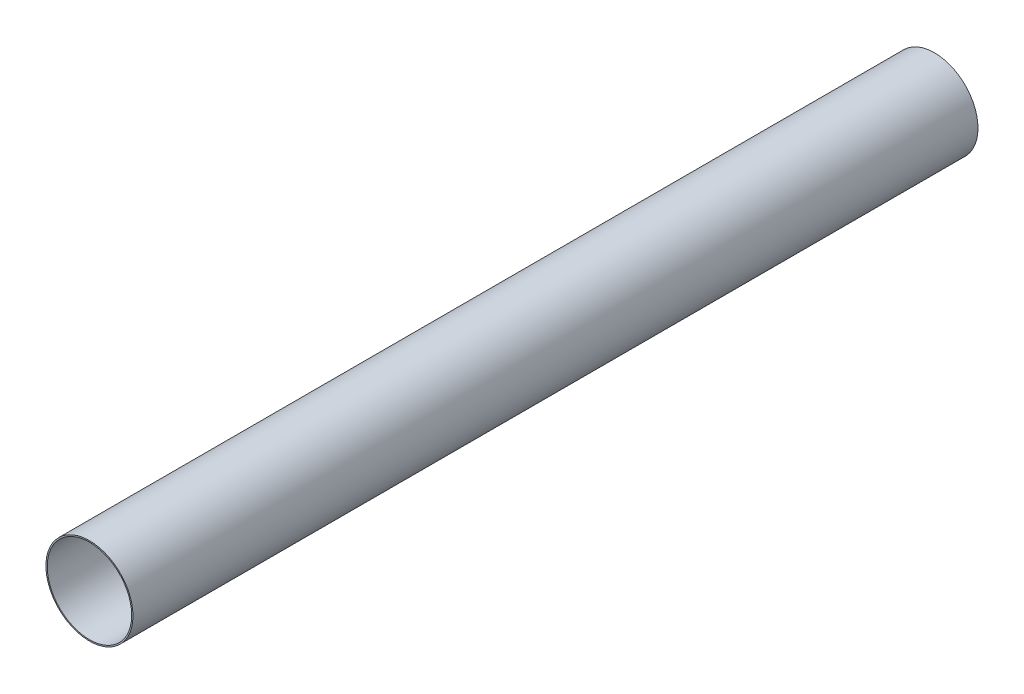
SolidWorks part; units mm, degrees
ref_plane "Front Plane" through (0, 0, 0) normal (0, 0, 1) x (1, 0, 0)
ref_plane "Top Plane" through (0, 0, 0) normal (0, 1, 0) x (1, 0, 0)
ref_plane "Right Plane" through (0, 0, 0) normal (1, 0, 0) x (0, 0, -1)
sketch "Sketch1" plane through (0, 0, 0) normal (0, 0, 1) x (1, 0, 0)
  circle A0 centre (0, 0) radius 39.2557
  circle A1 centre (0, 0) radius 38.1
  dimension "D1" = 76.2
  dimension "D2" = 78.5114
extrude "Boss-Extrude1" add sketch "Sketch1" along normal mid plane 762
equation "\"AIRFRAME_OD\"= 3.091in"
equation "\"AIRFRAME_ID\"= 3.00in"
equation "\"FLAT_T\"= 0.125in"
equation "\"NOSE_EXP_L\"= 3.5in"
equation "\"NOSE_SHOULDER_L\"= 5in"
equation "\"MAIN_L\"= 30in"
equation "\"RECO_COUP_L\"= 6in"
equation "\"RECO_SWITCH_L\"= 1.5in"
equation "\"DROGUE_L\"= 14in"
equation "\"ATS_FORE_COUP_L\"= 4in"
equation "\"ATS_AFT_COUP_L\"= 2.5in"
equation "\"LOWER_L\"= 16in"
equation "\"FIN_N\"= 4"
equation "\"CR_AFT_X\"= 0.5in"
equation "\"CR_FORE_X\"= 6in"
equation "\"D1@Sketch1\"=\"AIRFRAME_ID\""
equation "\"D2@Sketch1\"=\"AIRFRAME_OD\""
equation "\"D1@Boss-Extrude1\"=\"MAIN_L\""
equation "\"FIN_ROOT\"= 5in"
equation "\"FIN_X\"= 0.75in"
equation "\"MOTOR_OD\"= 2.25in"
equation "\"MOTOR_ID\"= 2.126in"
